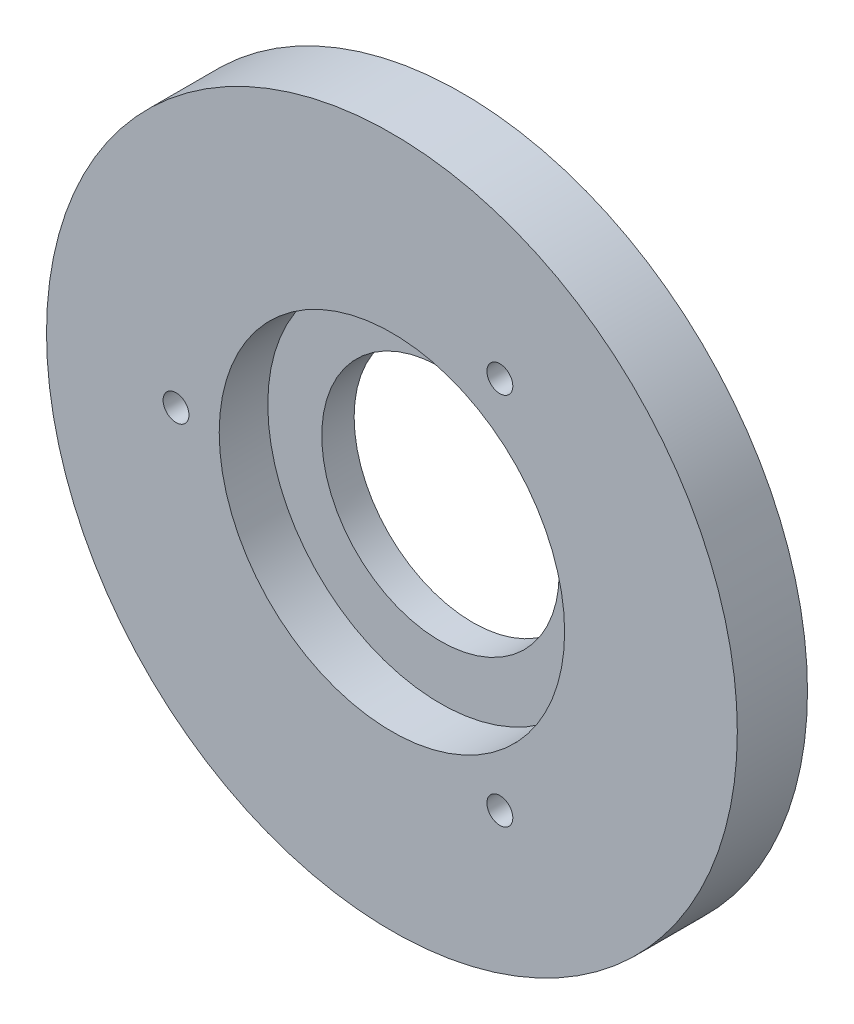
SolidWorks part; units mm, degrees
ref_plane "前视基准面" through (0, 0, 0) normal (0, 0, 1) x (1, 0, 0)
ref_plane "上视基准面" through (0, 0, 0) normal (0, 1, 0) x (1, 0, 0)
ref_plane "右视基准面" through (0, 0, 0) normal (1, 0, 0) x (0, 0, -1)
sketch "草图1" plane through (0, 0, 0) normal (0, 0, 1) x (1, 0, 0)
  circle A0 centre (0, 0) radius 16
extrude "凸台-拉伸1" add sketch "草图1" along normal blind 9
sketch "草图2" plane through (0, 0, 9) normal (0, 0, 1) x (1, 0, 0)
  circle A0 centre (0, 0) radius 6
extrude "凸台-拉伸2" add sketch "草图2" along normal blind 0.5
sketch "草图3" plane through (0, 0, 9.5) normal (0, 0, 1) x (1, 0, 0)
  circle A0 centre (0, 0) radius 16
extrude "凸台-拉伸3" add sketch "草图3" along normal blind 3.25
sketch "草图4" plane through (0, 0, 12.75) normal (0, 0, 1) x (1, 0, 0)
  circle A0 centre (0, 0) radius 5.5
extrude "凸台-拉伸4" add sketch "草图4" along normal blind 2.25
sketch "草图5" plane through (0, 0, 15) normal (0, 0, 1) x (1, 0, 0)
  circle A0 centre (0, 0) radius 3
extrude "切除-拉伸1" cut sketch "草图5" against normal blind 26.25
sketch "草图6" plane through (0, 0, 12.75) normal (0, 0, 1) x (1, 0, 0)
  circle A0 centre (0, 0) radius 5.5
  circle A1 centre (0, 0) radius 8
extrude "切除-拉伸2" cut sketch "草图6" against normal blind 2.25
sketch "草图7" plane through (0, 0, 0) normal (0, 0, -1) x (-1, 0, 0)
  circle A1 centre (8.6603, 5) radius 0.6
  circle A2 centre (-8.6603, 5) radius 0.6
  circle A3 centre (0, -10) radius 0.6
extrude "切除-拉伸3" cut sketch "草图7" against normal blind 6
sketch "草图8" plane through (0, 0, 12.75) normal (0, 0, 1) x (1, 0, 0)
  circle A2 centre (5, -8.6603) radius 0.6
  circle A3 centre (5, 8.6603) radius 0.6
  circle A4 centre (-10, 0) radius 0.6
extrude "切除-拉伸4" cut sketch "草图8" against normal blind 3
sketch "草图9" plane through (0, 0, 0) normal (0, 0, -1) x (-1, 0, 0)
  circle A0 centre (0, 0) radius 28.809
extrude "切除-拉伸5" cut sketch "草图9" against normal blind 9
sketch "草图10" plane through (0, 0, 15) normal (0, 0, 1) x (1, 0, 0)
  circle A0 centre (0, 0) radius 5.5
extrude "切除-拉伸6" cut sketch "草图10" against normal blind 9
